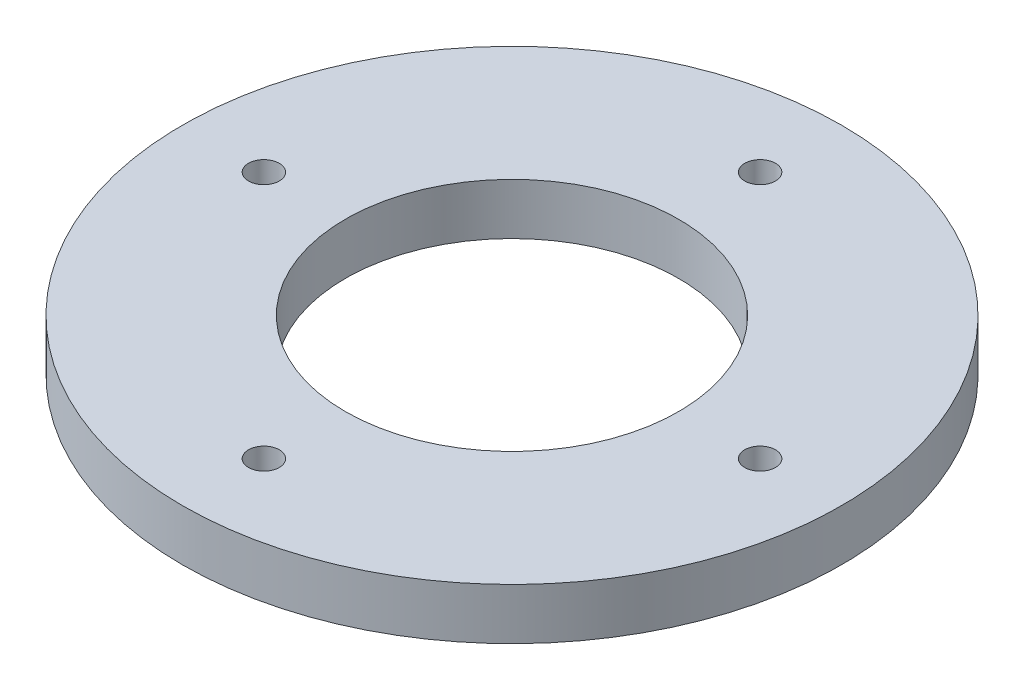
SolidWorks part; units mm, degrees
ref_plane "Front Plane" through (0, 0, 0) normal (0, 0, 1) x (1, 0, 0)
ref_plane "Top Plane" through (0, 0, 0) normal (0, 1, 0) x (1, 0, 0)
ref_plane "Right Plane" through (0, 0, 0) normal (1, 0, 0) x (0, 0, -1)
sketch "Sketch1" plane through (0, 0, 0) normal (0, 1, 0) x (1, 0, 0)
  circle A0 centre (0, 0) radius 32.135
  circle A1 centre (0, 0) radius 16.25
  dimension "D1" = 64.27
  dimension "D2" = 32.5
extrude "Boss-Extrude1" add sketch "Sketch1" along normal mid plane 5
sketch "Sketch2" plane through (0, 2.5, 0) normal (0, 1, 0) x (1, 0, 0)
  line L0 (0, 16.25) -> (0, 32.135) construction
  circle A0 centre (0, 24.1925) radius 1.5
  circle A1 centre (0, 0) radius 16.25 construction
  circle A2 centre (0, 0) radius 32.135 construction
  dimension "D1" = 3
extrude "Cut-Extrude1" cut sketch "Sketch2" against normal through all
pattern_circular "CirPattern1" count 4 over 360 about axis through (0, 0, 0) along (0, 1, 0) of "Cut-Extrude1"
